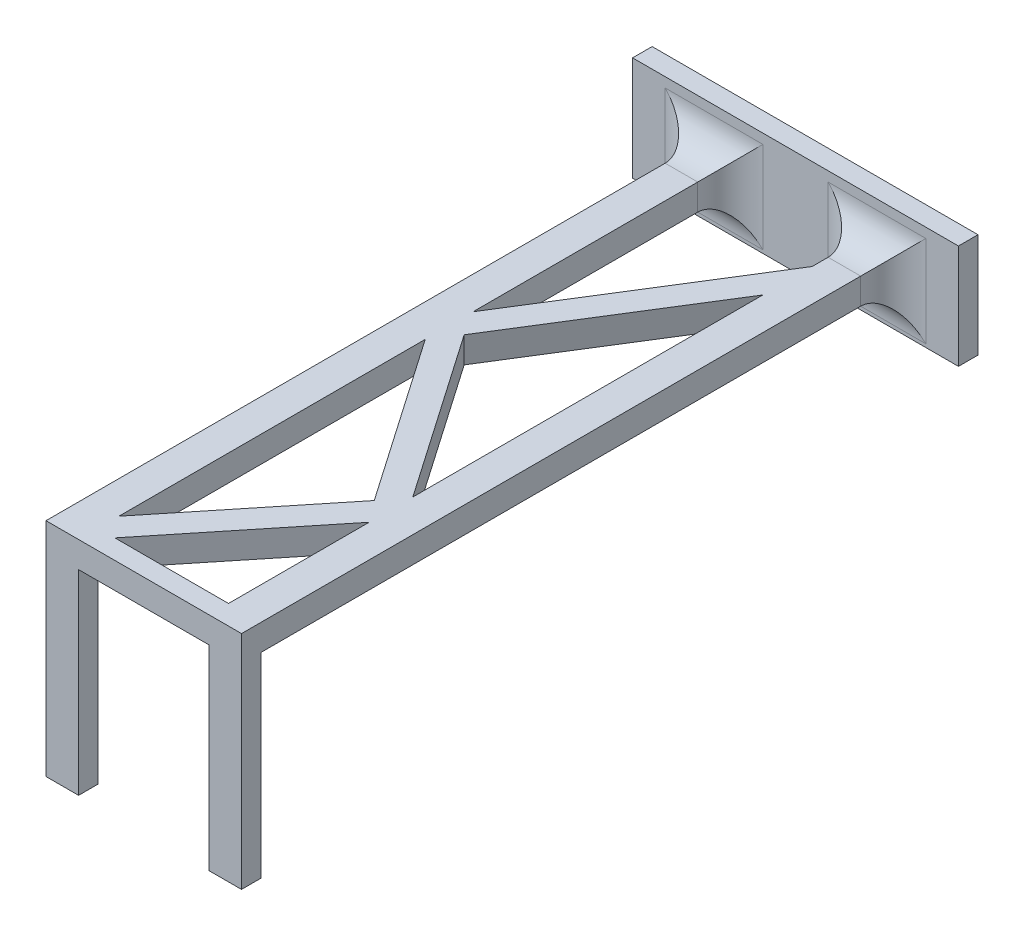
SolidWorks part; units mm, degrees
ref_plane "前视基准面" through (0, 0, 0) normal (0, 0, 1) x (1, 0, 0)
ref_plane "上视基准面" through (0, 0, 0) normal (0, 1, 0) x (1, 0, 0)
ref_plane "右视基准面" through (0, 0, 0) normal (1, 0, 0) x (0, 0, -1)
other "Configuration Table"
sketch "草图1" plane through (0, 0, 0) normal (0, 0, 1) x (1, 0, 0)
  line L1 (-22.149, 8.3709) -> (37.851, 8.3709)
  line L2 (-22.149, 8.3709) -> (-22.149, -7.6291)
  line L3 (-22.149, -7.6291) -> (37.851, -7.6291)
  line L4 (37.851, 8.3709) -> (37.851, -7.6291)
  dimension "D1" = 60
  dimension "D2" = 16
extrude "凸台-拉伸1" add sketch "草图1" along normal blind 3
sketch "草图2" plane through (0, 0, 3) normal (0, 0, 1) x (1, 0, 0)
  line L0 (-22.149, 8.3709) -> (-22.149, -7.6291) construction
  line L1 (-22.149, 1.8709) -> (37.851, 1.8709)
  line L2 (-22.149, 1.8709) -> (-22.149, -2.1291)
  line L3 (-22.149, -2.1291) -> (37.851, -2.1291)
  line L4 (37.851, 1.8709) -> (37.851, -2.1291)
  line L5 (37.851, -7.6291) -> (37.851, 8.3709) construction
  line L6 (-22.149, -7.6291) -> (37.851, -7.6291) construction
  dimension "D1" = 4
  dimension "D2" = 5.5
extrude "凸台-拉伸2" add sketch "草图2" along normal blind 100
sketch "草图3" plane through (0, -2.1291, 0) normal (0, -1, 0) x (1, 0, 0)
  line L0 (-22.149, 103) -> (37.851, 103) construction
  line L1 (-7.149, 103) -> (-2.149, 103)
  line L2 (-7.149, 103) -> (-7.149, 100)
  line L3 (-7.149, 100) -> (-2.149, 100)
  line L4 (22.851, 103) -> (22.851, 100)
  line L5 (-2.149, 103) -> (-2.149, 100)
  line L6 (17.851, 103) -> (17.851, 100)
  line L7 (17.851, 103) -> (22.851, 103)
  line L8 (17.851, 100) -> (22.851, 100)
  line L9 (-22.149, 103) -> (-22.149, 3) construction
  dimension "D1" = 20
  dimension "D2" = 30
  dimension "D3" = 5
  dimension "D4" = 3
  dimension "D5" = 15
extrude "凸台-拉伸3" add sketch "草图3" along normal blind 30
sketch "草图4" plane through (0, -2.1291, 0) normal (0, -1, 0) x (1, 0, 0)
  line L0 (-22.149, 3) -> (37.851, 3) construction
  line L1 (-22.149, 103) -> (-7.149, 103)
  line L2 (-22.149, 103) -> (-22.149, 3)
  line L3 (-22.149, 3) -> (-7.149, 3)
  line L4 (-7.149, 103) -> (-7.149, 3)
  line L5 (-2.149, 100) -> (17.851, 75.2336)
  line L10 (22.851, 103) -> (37.851, 103)
  line L11 (22.851, 103) -> (22.851, 3)
  line L12 (22.851, 3) -> (37.851, 3)
  line L13 (37.851, 103) -> (37.851, 3)
  line L14 (-7.149, 103) -> (-7.149, 100) construction
  line L15 (17.851, 75.2336) -> (-2.1613, 46.2747)
  line L16 (-2.149, 96.8166) -> (-2.149, 49.8104)
  line L17 (-22.149, 3) -> (37.851, 3) construction
  line L18 (17.851, 100) -> (17.851, 78.4169)
  line L19 (17.851, 100) -> (0.4217, 100)
  line L20 (-2.1613, 46.2747) -> (17.851, 14.2361)
  line L21 (-2.149, 96.8166) -> (15.3555, 75.1404)
  line L22 (15.3555, 75.1404) -> (-2.149, 49.8104)
  line L23 (-2.149, 42.4798) -> (16.1547, 13.1765)
  line L24 (0.4217, 100) -> (17.851, 78.4169)
  line L25 (17.851, 71.7156) -> (0.2314, 46.2192)
  line L26 (0.2314, 46.2192) -> (17.851, 18.0113)
  line L27 (-0.5931, 101.2565) -> (20.3464, 75.3267) construction
  line L28 (-3.705, 98.7435) -> (15.3555, 75.1404) construction
  line L29 (20.3464, 75.3267) -> (0.2314, 46.2192) construction
  line L30 (17.851, 71.7156) -> (17.851, 18.0113)
  line L31 (15.3555, 75.1404) -> (-4.5541, 46.3302) construction
  line L32 (-2.149, 42.4798) -> (-2.149, 3)
  line L33 (-4.5541, 46.3302) -> (16.1547, 13.1765) construction
  line L34 (0.2314, 46.2192) -> (19.5472, 15.2956) construction
  line L35 (17.851, 10.4609) -> (17.851, 3)
  line L36 (16.1547, 13.1765) -> (17.851, 10.4609)
  line L37 (-2.149, 3) -> (17.851, 3)
  line M9 (-7.149, 100) -> (-7.149, 103)
  line M10 (-7.149, 103) -> (-22.149, 103)
  line M11 (-22.149, 103) -> (-22.149, 3)
  line M12 (-22.149, 3) -> (37.851, 3)
  line M13 (37.851, 3) -> (37.851, 103)
  line M14 (37.851, 103) -> (22.851, 103)
  line M15 (22.851, 103) -> (22.851, 100)
  dimension "D1" = 2
  dimension "D2" = 2
extrude "切除-拉伸2" cut sketch "草图4" against normal blind 12 contours L4 M9 M10 M11 M12 | L36 L23 L32 L35 M12 | L30 L25 L26 | L22 L21 L16 | L11 M15 M12 M13 M14 | L18 L24 L19
fillet "圆角2" radius 5 8 edges at (22.851, -0.1291, 3) (20.351, -2.1291, 3) (-2.149, -0.1291, 3) (-4.649, -2.1291, 3) (-7.149, -0.1291, 3) (-4.649, 1.8709, 3) (17.851, -0.1291, 3) (20.351, 1.8709, 3)
sketch "草图6" plane through (0, 0, 3) normal (0, 0, 1) x (1, 0, 0)
  line L0 (-22.149, -7.6291) -> (37.851, -7.6291) construction
  line L1 (-22.149, 8.3709) -> (-17.149, 8.3709)
  line L2 (-22.149, 8.3709) -> (-22.149, -7.6291)
  line L3 (-22.149, -7.6291) -> (-17.149, -7.6291)
  line L4 (-17.149, 8.3709) -> (-17.149, -7.6291)
  line L6 (37.851, 8.3709) -> (32.851, 8.3709)
  line L7 (37.851, 8.3709) -> (37.851, -7.6291)
  line L8 (37.851, -7.6291) -> (32.851, -7.6291)
  line L9 (32.851, 8.3709) -> (32.851, -7.6291)
  dimension "D1" = 5
  dimension "D2" = 5
extrude "切除-拉伸3" cut sketch "草图6" against normal blind 12
